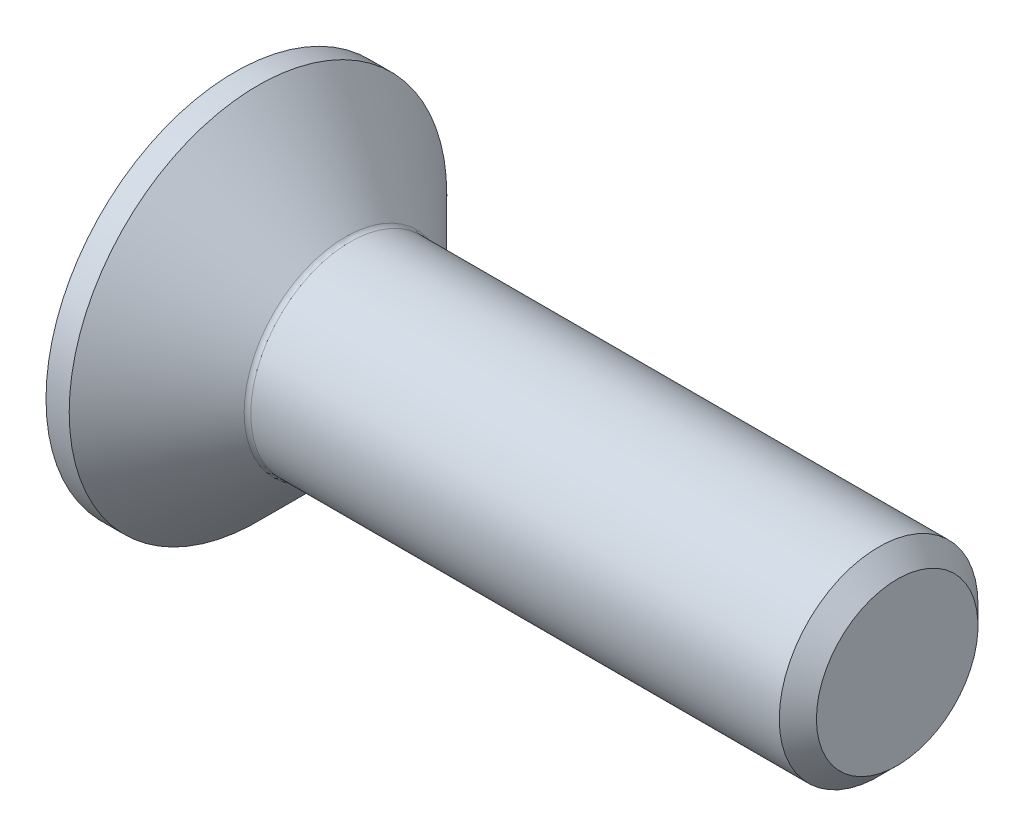
SolidWorks part; units mm, degrees
ref_plane "Plane1" through (0, 0, 0) normal (0, 0, 1) x (1, 0, 0)
ref_plane "Plane2" through (0, 0, 0) normal (0, 1, 0) x (1, 0, 0)
ref_plane "Plane3" through (0, 0, 0) normal (1, 0, 0) x (0, 0, -1)
sketch "BodySke" plane through (0, 0, 0) normal (0, 0, 1) x (1, 0, 0)
  line L0 (0, 0) -> (0, 2.85)
  line L1 (0.35, 2.85) -> (1.7, 1.5)
  line L2 (0, 2.85) -> (0.35, 2.85)
  line L3 (1.7, 1.5) -> (9.7195, 1.5)
  line L4 (10, 1.2195) -> (10, 0)
  line L5 (10, 0) -> (0, 0)
  line L6 (0, 0) -> (127, 0) construction
  line L7 (0.35, -2.85) -> (1.7, -1.5) construction
  line L8 (10, 1.2195) -> (9.7195, 1.5)
  line L9 (0, -2.85) -> (0.35, -2.85) construction
  line L10 (10, -1.2195) -> (9.7195, -1.5) construction
  line L11 (2.2, 7.85) -> (2.2, -14.375) construction
  line L12 (0, 16.35) -> (0, -5.875) construction
  dimension "Diameter" = 3
  dimension "Head_ht" = 1.7
  dimension "Length" = 10
  dimension "Body_ch_ang" = 45
  dimension "Head_dia" = 5.7
  dimension "Minor_dia" = 2.439
  dimension "Head_ang" = 90
  dimension "Advance" = 0.5
  dimension "Thread_nom" = 10
revolve "BaseBody" add sketch "BodySke" angle 360 about L6
cosmetic thread "ThreadCosmetic" parameters "Thread_length"=7.55, "Thread_minor"=2.439
fillet "Fillet1" radius 0.1 1 edges at (1.7, 0, 1.5)
sketch "Sketch2" plane through (0, 0, 0) normal (0, 0, 1) x (1, 0, 0)
  line L0 (0, 1.01) -> (1.2, 1.01)
  line L1 (1.2, 1.01) -> (1.7831, 0)
  line L2 (0, 0) -> (127, 0) construction
  line L3 (1.7831, 0) -> (0, 0)
  line L4 (0, 0) -> (0, 1.01)
  line L5 (0, -1.01) -> (1.2, -1.01) construction
  line L6 (0, 0) -> (47.625, 0) construction
  line L8 (0, 2.85) -> (0, -2.85) construction
  dimension "D2" = 60
  dimension "PreBroach_depth" = 1.2
  dimension "PreBroach_dia" = 2.02
revolve "PreBroach" cut sketch "Sketch2" angle 360 about L6
sketch "Sketch3" plane through (0, 0, 0) normal (-1, 0, 0) x (0, 0, 1)
  line L0 (-1.01, -0.5831) -> (-1.01, 0.5831)
  line L1 (-1.01, 0.5831) -> (0, 1.1662)
  line L2 (0, 1.1662) -> (1.01, 0.5831)
  line L3 (1.01, 0.5831) -> (1.01, -0.5831)
  line L4 (1.01, -0.5831) -> (0, -1.1662)
  line L5 (0, -1.1662) -> (-1.01, -0.5831)
  dimension "D1" = 1.01
  dimension "D2" = 1.01
  dimension "D3" = 2.02
  dimension "Hex_size" = 2.02
extrude "Hex" cut sketch "Sketch3" against normal blind 1.2
sketch "ThdSchSke" plane through (0, 0, 0) normal (0, 0, 1) x (1, 0, 0)
  line L0 (2.45, -1.2195) -> (2.2536, -1.5)
  line L1 (2.45, -1.2195) -> (2.6464, -1.5)
  line L2 (2.6464, -1.5) -> (2.6464, -1.875)
  line L3 (-3.175, 0) -> (5.1513, 0) construction
  line L4 (0, 2.85) -> (0, -2.85) construction
  line L5 (2.6464, -1.875) -> (2.2536, -1.875)
  line L6 (2.2536, -1.875) -> (2.2536, -1.5)
  dimension "Thread_minor" = 2.439
  dimension "Diameter" = 3
  dimension "Start" = 2.45
  dimension "SideAngle" = 55
  dimension "VeeAngle" = 70
  dimension "Overcut" = 3.75
revolve "ThreadSchematic" [suppressed] cut sketch "ThdSchSke" angle 360 about L3
pattern_linear "ThdSchPat" [suppressed]
equation "\"Thread_minor@ThreadCosmetic\"  =  \"Minor_dia@BodySke\""
equation "\"D1@Sketch3\" = \"Hex_size@Sketch3\" / 2"
equation "\"D2@Sketch3\" = \"D1@Sketch3\""
equation "\"D3@Sketch3\" = \"Hex_size@Sketch3\""
equation "\"Thread_length@ThreadCosmetic\" = ((sgn( (\"Length@BodySke\" - \"Advance@BodySke\" * 1.5 - \"Head_ht@BodySke\" ) - \"Thread_nom@BodySke\" )-1)*( (\"Length@BodySke\" - \"Advance@BodySke\" * 1.5 - \"Head_ht@BodySke\" ) - \"Thread_nom@BodySke\" ))/-2+ \"Thread_nom@BodySke\""
equation "\"Thread_minor@ThdSchSke\" = \"Minor_dia@BodySke\""
equation "\"Diameter@ThdSchSke\" = \"Diameter@BodySke\""
equation "\"Overcut@ThdSchSke\" = \"Diameter@BodySke\" * 1.25"
equation "\"Start@ThdSchSke\" = 0.000001 + \"Length@BodySke\" - \"Thread_length@ThreadCosmetic\"  '---Countersunk---"
equation "\"Num_threads@ThdSchPat\" = int( \"Thread_length@ThreadCosmetic\" / \"Advance@BodySke\" + 0.999 )  + 1"
equation "\"Advance@ThdSchPat\" = \"Thread_length@ThreadCosmetic\" /  (\"Num_threads@ThdSchPat\" - 1) 'relax it"
equation "\"Num_threads@ThdSchPat\" = \"Num_threads@ThdSchPat\" - sgn( \"Num_threads@ThdSchPat\" - 1) '---chamfered tips only---"
